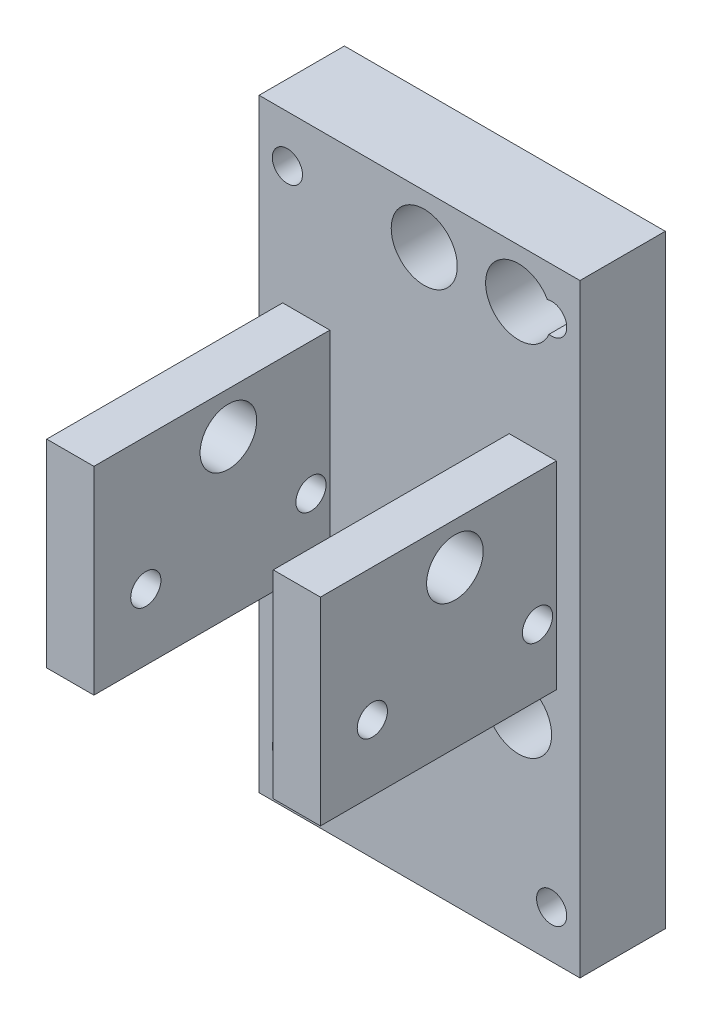
SolidWorks part; units mm, degrees
ref_plane "Front Plane" through (0, 0, 0) normal (0, 0, 1) x (1, 0, 0)
ref_plane "Top Plane" through (0, 0, 0) normal (0, 1, 0) x (1, 0, 0)
ref_plane "Right Plane" through (0, 0, 0) normal (1, 0, 0) x (0, 0, -1)
sketch "Sketch1" plane through (0, 0, 0) normal (0, 0, 1) x (1, 0, 0)
  line L1 (-17, -32) -> (17, -32)
  line L2 (-17, -32) -> (-17, 32)
  line L3 (-17, 32) -> (17, 32)
  line L4 (17, -32) -> (17, 32)
  line L5 (-17, -32) -> (17, 32) construction
  line L6 (-17, 32) -> (17, -32) construction
  point P0 (0, 0)
  dimension "D1" = 64
  dimension "D2" = 34
extrude "Boss-Extrude1" add sketch "Sketch1" along normal blind 9.04
sketch "Sketch2" plane through (0, 0, 9.04) normal (0, 0, 1) x (1, 0, 0)
  line L0 (-9.5, 32) -> (-9.5, -32) construction
  line L1 (17, 32) -> (-17, 32) construction
  line L2 (-17, -32) -> (17, -32) construction
  line L3 (9.5, 32) -> (9.5, -32) construction
  line L5 (-17, 32) -> (-17, -32) construction
  line L7 (9.5, 14.2) -> (14.5, 14.2)
  line L8 (14.5, 14.2) -> (14.5, -6.8)
  line L9 (14.5, -6.8) -> (9.5, -6.8)
  line L10 (-17, 0.2) -> (17, 0.2) construction
  line L11 (17, -32) -> (17, 32) construction
  line L12 (9.5, 14.2) -> (9.5, -6.8)
  line L13 (0, -32) -> (0, 32) construction
  line L14 (-9.5, 14.2) -> (-14.5, 14.2)
  line L15 (-14.5, 14.2) -> (-14.5, -6.8)
  line L16 (-14.5, -6.8) -> (-9.5, -6.8)
  line L17 (-9.5, 14.2) -> (-9.5, -6.8)
  dimension "D1" = 19
  dimension "D2" = 7.5
  dimension "D3" = 31.8
  dimension "D4" = 14
  dimension "D5" = 7
  dimension "D6" = 5
extrude "Boss-Extrude2" add sketch "Sketch2" along normal blind 25
sketch "Sketch3" plane through (14.5, 0, 0) normal (1, 0, 0) x (0, 0, -1)
  line L0 (-34.04, 0.2) -> (-9.04, 0.2) construction
  line L1 (-34.04, -6.8) -> (-34.04, 14.2) construction
  line L2 (-9.04, -6.8) -> (-9.04, 14.2) construction
  line L3 (-34.04, -6.8) -> (-9.04, -6.8) construction
  circle A0 centre (-28.54, 0.2) radius 1.6
  circle A1 centre (-11.04, 0.2) radius 1.6
  circle A2 centre (-19.79, 9.8) radius 3
  dimension "D2" = 3.2
  dimension "D3" = 3.2
  dimension "D8" = 6
  dimension "D1" = 7
  dimension "D4" = 2
  dimension "D5" = 17.5
  dimension "D6" = 9.6
  dimension "D7" = 8.75
extrude "Cut-Extrude1" cut sketch "Sketch3" against normal blind 30
sketch "Sketch4" plane through (0, 0, 9.04) normal (0, 0, 1) x (1, 0, 0)
  line L0 (0, -32) -> (0, 32) construction
  line L3 (-17, -32) -> (17, -32) construction
  line L4 (17, 32) -> (-17, 32) construction
  line L5 (-17, 0) -> (17, 0) construction
  line L6 (-17, 32) -> (-17, -32) construction
  line L7 (17, -32) -> (17, 32) construction
  circle A0 centre (-14, -27) radius 1.6
  circle A4 centre (-14, 27) radius 1.6
  circle A5 centre (14, -27) radius 1.6
  circle A6 centre (14, 27) radius 1.6
  dimension "D1" = 3.2
  dimension "D2" = 5
  dimension "D3" = 3
extrude "Cut-Extrude2" cut sketch "Sketch4" against normal blind 10
sketch "Sketch5" plane through (0, 0, 0) normal (0, 0, -1) x (-1, 0, 0)
  line L0 (-17, 32) -> (17, 32) construction
  line L1 (17, 32) -> (17, -32) construction
  line L2 (-5.5, 32) -> (-5.5, -32) construction
  line L3 (17, -32) -> (-17, -32) construction
  line L4 (-17, 7.8) -> (17, 7.8) construction
  line L5 (-17, -32) -> (-17, 32) construction
  circle A0 centre (-0.5, 26.8) radius 3.5
  circle A1 centre (-10.5, 26.8) radius 3.5
  circle A2 centre (-0.5, -11.2) radius 3.5
  circle A3 centre (-10.5, -11.2) radius 3.5
  dimension "D2" = 7
  dimension "D3" = 6.5
  dimension "D1" = 5.2
  dimension "D4" = 5
  dimension "D5" = 19
extrude "Cut-Extrude3" cut sketch "Sketch5" against normal blind 10
